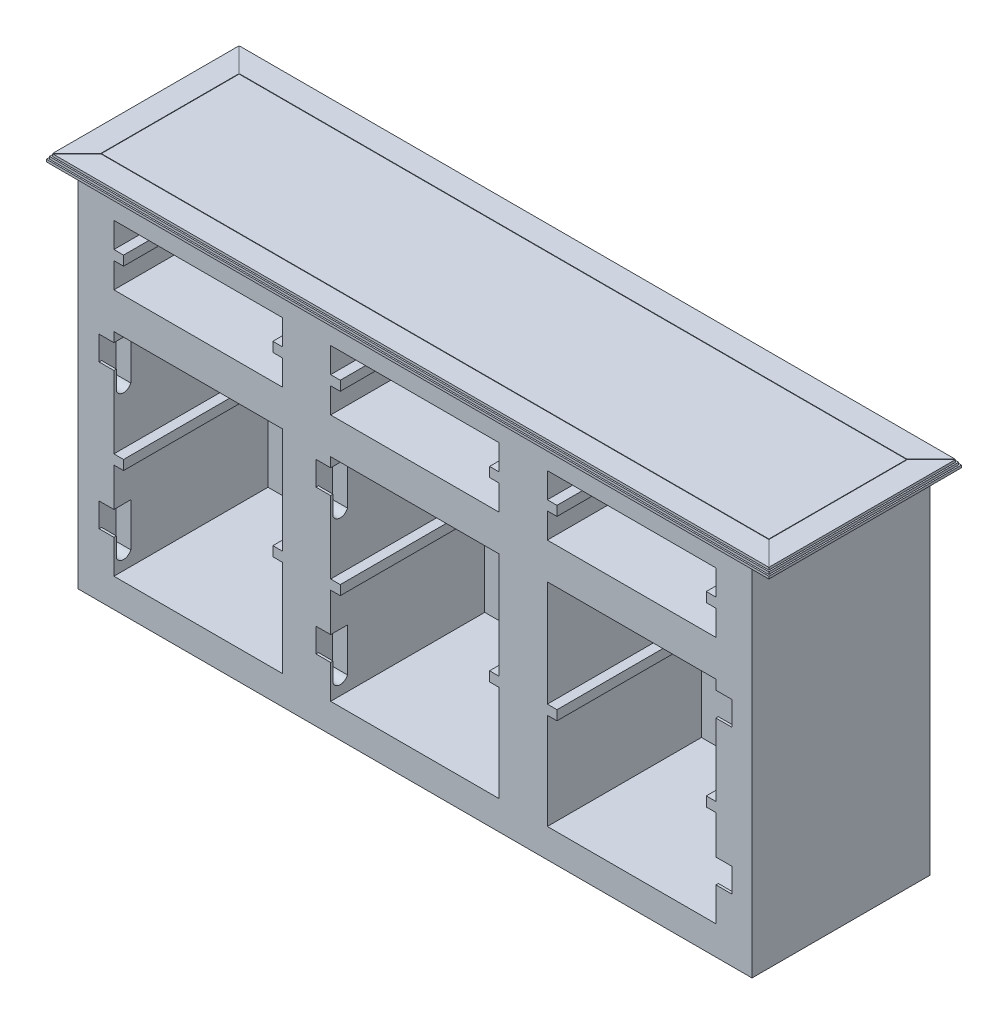
SolidWorks part; units mm, degrees
material "Mahogany"
ref_plane "Front Plane" through (0, 0, 0) normal (0, 0, 1) x (1, 0, 0)
ref_plane "Top Plane" through (0, 0, 0) normal (0, 1, 0) x (1, 0, 0)
ref_plane "Right Plane" through (0, 0, 0) normal (1, 0, 0) x (0, 0, -1)
sketch "Sketch1" plane through (0, 0, 0) normal (0, 1, 0) x (1, 0, 0)
  line L1 (750, 200) -> (-750, 200)
  line L2 (750, 200) -> (750, -200)
  line L3 (750, -200) -> (-750, -200)
  line L4 (-750, 200) -> (-750, -200)
  line L5 (750, 200) -> (-750, -200) construction
  line L6 (750, -200) -> (-750, 200) construction
  point P0 (0, 0)
  dimension "D1" = 1500
  dimension "D2" = 400
extrude "Boss-Extrude1" add sketch "Sketch1" along normal blind 5
sketch "Sketch3" plane through (0, 5, 0) normal (0, 1, 0) x (1, 0, 0)
  line L8 (-747, 197) -> (-747, -197)
  line L9 (-747, -197) -> (747, -197)
  line L10 (747, -197) -> (747, 197)
  line L11 (747, 197) -> (-747, 197)
  line L12 (-747, 197) -> (-747, -197)
  line L13 (-747, -197) -> (747, -197)
  line L14 (747, -197) -> (747, 197)
  line L15 (747, 197) -> (-747, 197)
  dimension "D1" = 3
extrude "Boss-Extrude3" add sketch "Sketch3" along normal blind 5
sketch "Sketch4" plane through (0, 10, 0) normal (0, 1, 0) x (1, 0, 0)
  line L8 (744, 194) -> (-744, 194)
  line L9 (-744, 194) -> (-744, -194)
  line L10 (-744, -194) -> (744, -194)
  line L11 (744, -194) -> (744, 194)
  line L12 (744, 194) -> (-744, 194)
  line L13 (-744, 194) -> (-744, -194)
  line L14 (-744, -194) -> (744, -194)
  line L15 (744, -194) -> (744, 194)
  dimension "D1" = 3
extrude "Boss-Extrude4" add sketch "Sketch4" along normal blind 5
sketch "Sketch6" plane through (0, 15, 0) normal (0, 1, 0) x (1, 0, 0)
  line L1 (744, 194) -> (743, 194)
  line L2 (744, 193) -> (744, 194)
  line L3 (694, 143) -> (744, 193)
  line L4 (-743, 194) -> (-693, 144)
  line L5 (744, 194) -> (-744, 194) construction
  line L6 (-694, 143) -> (-744, 193)
  line L7 (-744, 194) -> (-744, -194) construction
  line L8 (694, -144) -> (694, 144)
  line L9 (694, 144) -> (-694, 144)
  line L10 (-694, 144) -> (-694, -144)
  line L11 (-694, -144) -> (694, -144)
  line L12 (694, -143) -> (694, 143)
  line L13 (693, 144) -> (-693, 144)
  line L14 (-694, 143) -> (-694, -143)
  line L15 (-693, -144) -> (693, -144)
  line L16 (-744, 193) -> (-744, 194)
  line L17 (-744, 194) -> (-743, 194)
  line L18 (743, 194) -> (693, 144)
  line L20 (-694, -143) -> (-744, -193)
  line L21 (-743, -194) -> (-693, -144)
  line L22 (-744, -194) -> (-743, -194)
  line L23 (-744, -193) -> (-744, -194)
  line L24 (743, -194) -> (693, -144)
  line L25 (694, -143) -> (744, -193)
  line L26 (744, -193) -> (744, -194)
  line L27 (744, -194) -> (743, -194)
  line L29 (-693, 143) -> (693, 143)
  line L30 (-693, 143) -> (-693, -143)
  line L31 (-693, -143) -> (693, -143)
  line L32 (693, 143) -> (693, -143)
  dimension "D2" = 1
  dimension "D3" = 1
  dimension "D4" = 1
  dimension "D5" = 1
  dimension "D6" = 1
  dimension "D7" = 1
  dimension "D8" = 1
  dimension "D9" = 1
  dimension "D1" = 50
extrude "Cut-Extrude1" cut sketch "Sketch6" against normal blind 1
sketch "Sketch7" plane through (0, 0, 0) normal (0, -1, 0) x (1, 0, 0)
  line L0 (-750, -200) -> (-750, 200) construction
  line L1 (750, 200) -> (750, -200) construction
  line L2 (-700, -185) -> (700, -185)
  line L3 (750, -200) -> (-750, -200) construction
  line L6 (-750, 200) -> (750, 200) construction
  line L12 (-700, 185) -> (-700, -185)
  line L14 (700, -185) -> (700, 185)
  line L15 (700, 185) -> (-700, 185)
  dimension "D2" = 50
  dimension "D1" = 50
  dimension "D3" = 15
  dimension "D4" = 15
extrude "Boss-Extrude5" add sketch "Sketch7" along normal blind 750
sketch "Sketch8" plane through (0, 0, 185) normal (0, 0, 1) x (1, 0, 0)
  line L0 (-700, -750) -> (-700, 0) construction
  line L1 (-625, -250) -> (-275, -250)
  line L2 (-625, -250) -> (-625, -470)
  line L3 (-625, -690) -> (-275, -690)
  line L4 (-275, -250) -> (-275, -470)
  line L5 (-175, -250) -> (175, -250)
  line L6 (-175, -250) -> (-175, -470)
  line L7 (-175, -690) -> (175, -690)
  line L8 (175, -250) -> (175, -470)
  line L9 (275, -250) -> (625, -250)
  line L10 (275, -250) -> (275, -470)
  line L11 (275, -690) -> (625, -690)
  line L12 (625, -250) -> (625, -470)
  line L13 (700, -750) -> (700, 0) construction
  line L14 (700, 0) -> (-700, 0) construction
  line L15 (-625, -470) -> (-605, -470)
  line L17 (-625, -490) -> (-605, -490)
  line L18 (-605, -470) -> (-605, -490)
  line L19 (-175, -470) -> (-155, -470)
  line L21 (-175, -490) -> (-155, -490)
  line L22 (-155, -470) -> (-155, -490)
  line L23 (275, -470) -> (295, -470)
  line L25 (275, -490) -> (295, -490)
  line L26 (295, -470) -> (295, -490)
  line L27 (0, 220.9822) -> (0, -850.3183) construction
  line L28 (-625, -490) -> (-625, -690)
  line L29 (-175, -490) -> (-175, -690)
  line L30 (275, -490) -> (275, -690)
  line L31 (-450, -797.1707) -> (-450, 34.4488) construction
  line L32 (450, 104.4351) -> (450, -919.8611) construction
  line L34 (-275, -490) -> (-295, -490)
  line L35 (-295, -470) -> (-295, -490)
  line L36 (-275, -470) -> (-295, -470)
  line L37 (-275, -490) -> (-275, -690)
  line L38 (175, -490) -> (155, -490)
  line L39 (155, -470) -> (155, -490)
  line L40 (175, -470) -> (155, -470)
  line L41 (175, -490) -> (175, -690)
  line L42 (625, -490) -> (605, -490)
  line L43 (605, -470) -> (605, -490)
  line L44 (625, -470) -> (605, -470)
  line L45 (625, -490) -> (625, -690)
  line L46 (-625, -175) -> (-275, -175)
  line L47 (-625, -175) -> (-625, -122.5)
  line L48 (-625, -50) -> (-275, -50)
  line L49 (-275, -175) -> (-275, -122.5)
  line L50 (-175, -175) -> (175, -175)
  line L51 (-175, -175) -> (-175, -122.5)
  line L52 (-175, -50) -> (175, -50)
  line L58 (-275, -122.5) -> (-295, -122.5)
  line L59 (-625, -102.5) -> (-605, -102.5)
  line L61 (-625, -122.5) -> (-605, -122.5)
  line L62 (-605, -102.5) -> (-605, -122.5)
  line L63 (-295, -102.5) -> (-295, -122.5)
  line L64 (-275, -102.5) -> (-295, -102.5)
  line L66 (-625, -102.5) -> (-625, -50)
  line L67 (-275, -102.5) -> (-275, -50)
  line L68 (275, -102.5) -> (275, -50)
  line L69 (625, -50) -> (275, -50)
  line L70 (625, -102.5) -> (625, -50)
  line L71 (625, -102.5) -> (605, -102.5)
  line L72 (605, -102.5) -> (605, -122.5)
  line L73 (625, -122.5) -> (605, -122.5)
  line L74 (625, -175) -> (625, -122.5)
  line L75 (625, -175) -> (275, -175)
  line L76 (275, -175) -> (275, -122.5)
  line L77 (275, -122.5) -> (295, -122.5)
  line L78 (295, -102.5) -> (295, -122.5)
  line L79 (275, -102.5) -> (295, -102.5)
  line L80 (-175, -102.5) -> (-175, -50)
  line L81 (-175, -102.5) -> (-155, -102.5)
  line L83 (-175, -122.5) -> (-155, -122.5)
  line L84 (-155, -102.5) -> (-155, -122.5)
  line L85 (175, -175) -> (175, -122.5)
  line L86 (175, -122.5) -> (155, -122.5)
  line L87 (155, -102.5) -> (155, -122.5)
  line L88 (175, -102.5) -> (155, -102.5)
  line L89 (175, -102.5) -> (175, -50)
  point P57 (0, -175)
  point P58 (0, -175)
  point P59 (0, -50)
  point P89 (0, -50)
  dimension "D1" = 75
  dimension "D2" = 350
  dimension "D3" = 350
  dimension "D4" = 350
  dimension "D5" = 75
  dimension "D6" = 100
  dimension "D7" = 100
  dimension "D8" = 20
  dimension "D9" = 20
  dimension "D10" = 20
  dimension "D11" = 20
  dimension "D12" = 20
  dimension "D13" = 20
  dimension "D14" = 440
  dimension "D15" = 440
  dimension "D16" = 440
  dimension "D17" = 75
  dimension "D18" = 250
  dimension "D19" = 125
  dimension "D20" = 220
  dimension "D21" = 220
  dimension "D22" = 220
  dimension "D23" = 20
  dimension "D24" = 20
  dimension "D25" = 52.5
  dimension "D26" = 20
  dimension "D27" = 20
extrude "Cut-Extrude2" cut sketch "Sketch8" against normal blind 320
sketch "Sketch9" plane through (-625, 0, 0) normal (1, 0, 0) x (0, 0, -1)
  line L0 (-150, -270) -> (-150, -360)
  line L2 (-150, -270) -> (-185, -270)
  line L3 (-150, -570) -> (-150, -660)
  line L5 (-150, -570) -> (-185, -570)
  line L10 (135, -250) -> (-185, -250) construction
  line L11 (-185, -250) -> (-185, -470) construction
  line L12 (-150, -270) -> (-150, -670) construction
  line L13 (-185, -570) -> (-185, -620)
  line L14 (-180, -620) -> (-185, -620)
  line L15 (-180, -660) -> (-180, -620)
  line L16 (-185, -270) -> (-185, -320)
  line L17 (-180, -320) -> (-185, -320)
  line L18 (-180, -360) -> (-180, -320)
  arc A2 (-150, -660) -> (-180, -660) centre (-165, -653.75) cw
  arc A3 (-150, -360) -> (-180, -360) centre (-165, -353.75) cw
  point P1 (-165, -670)
  dimension "D3" = 40
  dimension "D4" = 16.25
  dimension "D15" = 16.25
  dimension "D18" = 216.25
  dimension "D1" = 400
  dimension "D2" = 50
  dimension "D5" = 35
  dimension "D6" = 30
  dimension "D7" = 83.75
  dimension "D8" = 20
  dimension "D9" = 35
  dimension "D10" = 35
  dimension "D11" = 30
  dimension "D12" = 50
  dimension "D13" = 40
  dimension "D14" = 83.75
  dimension "D16" = 90
  dimension "D17" = 90
extrude "Cut-Extrude3" cut sketch "Sketch9" against normal blind 30.65
sketch "Sketch10" plane through (-175, 0, 0) normal (1, 0, 0) x (0, 0, -1)
  line L0 (-150, -270) -> (-150, -360)
  line L1 (-150, -270) -> (-185, -270)
  line L2 (-150, -570) -> (-150, -660)
  line L3 (-150, -570) -> (-185, -570)
  line L4 (-150, -270) -> (-150, -660) construction
  line L5 (-185, -570) -> (-185, -620)
  line L6 (-180, -620) -> (-185, -620)
  line L7 (-180, -660) -> (-180, -620)
  line L8 (-185, -270) -> (-185, -320)
  line L9 (-180, -320) -> (-185, -320)
  line L10 (-180, -360) -> (-180, -320)
  line L11 (-185, -250) -> (-185, -470) construction
  line L12 (135, -250) -> (-185, -250) construction
  arc A0 (-150, -660) -> (-180, -660) centre (-165, -653.75) cw
  arc A1 (-150, -360) -> (-180, -360) centre (-165, -353.75) cw
  dimension "D6" = 16.25
  dimension "D10" = 16.25
  dimension "D7" = 216.25
  dimension "D1" = 35
  dimension "D2" = 20
  dimension "D3" = 83.75
  dimension "D4" = 50
  dimension "D5" = 30
  dimension "D8" = 35
  dimension "D9" = 30
  dimension "D11" = 83.75
  dimension "D12" = 40
  dimension "D13" = 50
  dimension "D14" = 50
  dimension "D15" = 40
  dimension "D16" = 90
  dimension "D17" = 90
extrude "Cut-Extrude4" cut sketch "Sketch10" against normal blind 30.65
sketch "Sketch12" plane through (625, 0, 0) normal (-1, 0, 0) x (0, 0, 1)
  line L0 (150, -270) -> (150, -360)
  line L1 (185, -270) -> (150, -270)
  line L2 (150, -570) -> (150, -660)
  line L3 (185, -570) -> (150, -570)
  line L4 (150, -270) -> (150, -660) construction
  line L11 (-135, -250) -> (185, -250) construction
  line L12 (185, -470) -> (185, -250) construction
  line L13 (180, -360) -> (180, -320)
  line L14 (180, -320) -> (185, -320)
  line L15 (185, -270) -> (185, -320)
  line L16 (180, -660) -> (180, -620)
  line L17 (180, -620) -> (185, -620)
  line L18 (185, -570) -> (185, -620)
  arc A2 (150, -360) -> (180, -360) centre (165, -353.75) ccw
  arc A3 (150, -660) -> (180, -660) centre (165, -653.75) ccw
  dimension "D14" = 90
  dimension "D15" = 90
  dimension "D17" = 20
  dimension "D18" = 35
extrude "Cut-Extrude6" cut sketch "Sketch12" against normal blind 33.56
